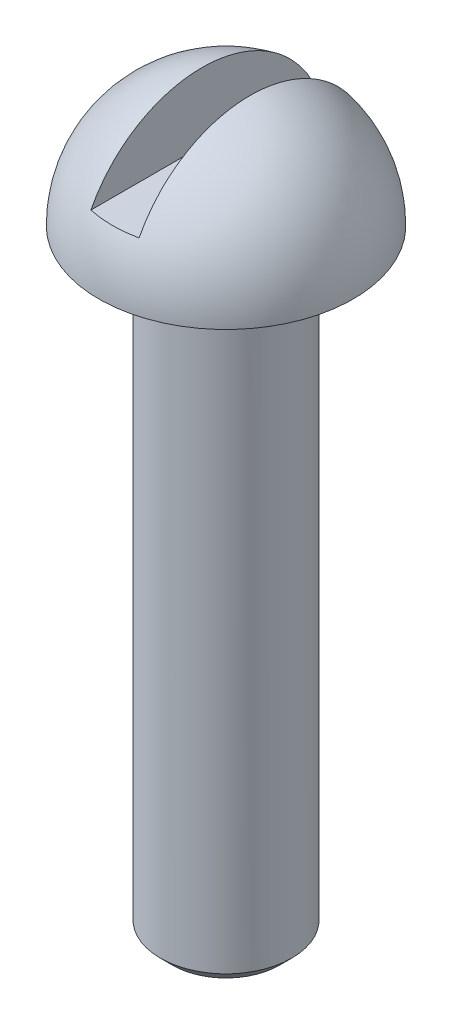
SolidWorks part; units mm, degrees
material "AISI 1020"
ref_plane "Спереди" through (0, 0, 0) normal (0, 0, 1) x (1, 0, 0)
ref_plane "Сверху" through (0, 0, 0) normal (0, 1, 0) x (1, 0, 0)
ref_plane "Справа" through (0, 0, 0) normal (1, 0, 0) x (0, 0, -1)
sketch "Эскиз1" plane through (0, 0, 0) normal (0, 0, 1) x (1, 0, 0)
  line L0 (2.9, 0) -> (1.5, 0)
  line L1 (1.5, 0) -> (1.5, -14)
  line L2 (1.5, -14) -> (0, -14)
  line L3 (0, 2.9) -> (0, -14) construction
  line L4 (0, 2.9) -> (0, -14)
  line L5 (0, 2.9) -> (0, -14)
  arc A0 (0, 2.9) -> (2.9, 0) centre (0, 0) cw
  dimension "D1" = 2.9
  dimension "D2" = 14
  dimension "D3" = 1.5
revolve "Повернуть1" add sketch "Эскиз1" angle 360 about L3
cosmetic thread "Условное изображение резьбы1" parameters "D1"=12, "D2"=2.439
chamfer "Фаска1" distance 0.2805 angle 45 1 edges at (-1.5, -14, 0)
sketch "Эскиз4" plane through (0, 0, 0) normal (0, 0, 1) x (1, 0, 0)
  line L1 (-0.55, 1.3) -> (0.55, 1.3)
  line L2 (-0.55, 1.3) -> (-0.55, 4.5)
  line L3 (-0.55, 4.5) -> (0.55, 4.5)
  line L4 (0.55, 1.3) -> (0.55, 4.5)
  line L5 (-0.55, 1.3) -> (0.55, 4.5) construction
  line L6 (-0.55, 4.5) -> (0.55, 1.3) construction
  arc A0 (2.9, 0) -> (-2.9, 0) centre (0, 0) ccw construction
  point P0 (0, 2.9)
  dimension "D1" = 1.6
  dimension "D2" = 1.1
extrude "Вырез-Вытянуть2" cut sketch "Эскиз4" against normal through all and the other way through all
